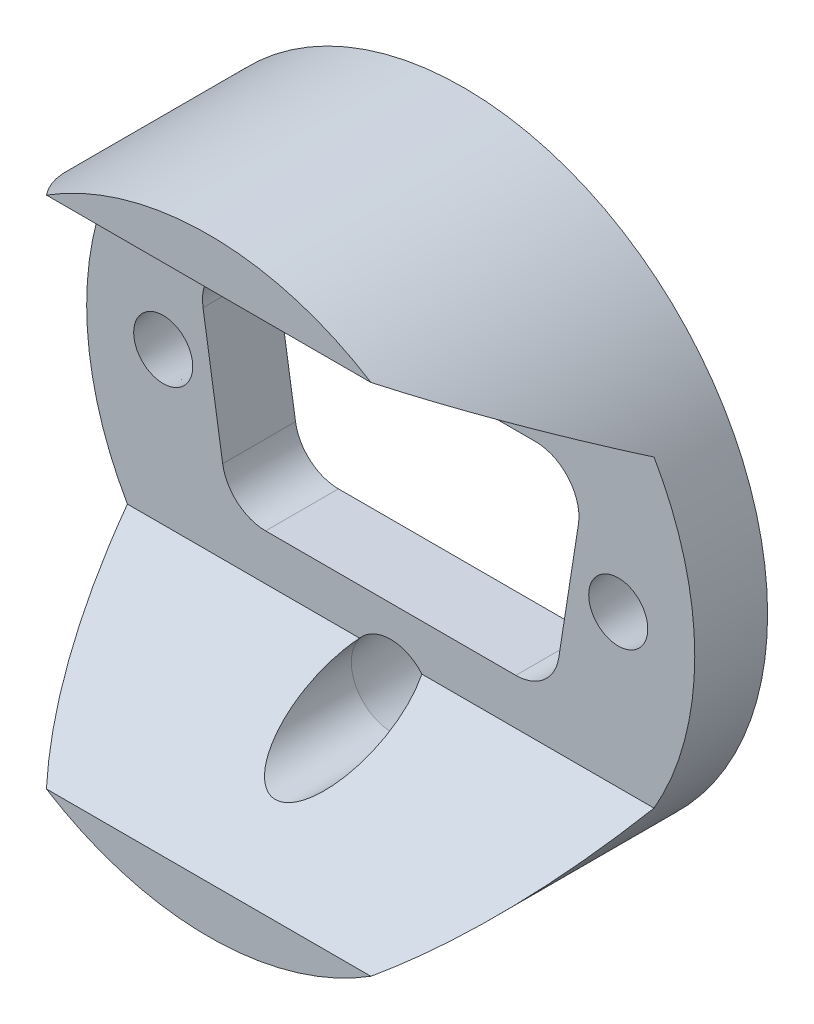
SolidWorks part; units mm, degrees
material "6061-T6 (SS)"
ref_plane "Front Plane" through (0, 0, 0) normal (0, 0, 1) x (1, 0, 0)
ref_plane "Top Plane" through (0, 0, 0) normal (0, 1, 0) x (1, 0, 0)
ref_plane "Right Plane" through (0, 0, 0) normal (1, 0, 0) x (0, 0, -1)
sketch "Sketch1" plane through (0, 0, 0) normal (0, 0, 1) x (1, 0, 0)
  circle A0 centre (0, 0) radius 16.7
  dimension "D1" = 33.4
extrude "Boss-Extrude1" add sketch "Sketch1" along normal blind 14
sketch "Sketch2" plane through (0, 0, 14) normal (0, 0, 1) x (1, 0, 0)
  line L1 (-19.05, -6.35) -> (19.05, -6.35)
  line L2 (-19.05, -6.35) -> (-19.05, 6.35)
  line L3 (-19.05, 6.35) -> (19.05, 6.35)
  line L4 (19.05, -6.35) -> (19.05, 6.35)
  line L5 (-19.05, -6.35) -> (19.05, 6.35) construction
  line L6 (-19.05, 6.35) -> (19.05, -6.35) construction
  point P0 (0, 0)
  dimension "D1" = 12.7
  dimension "D2" = 38.1
extrude "Cut-Extrude1" cut sketch "Sketch2" against normal blind 10
sketch "Sketch3" plane through (0, 0, 4) normal (0, 0, 1) x (1, 0, 0)
  line L0 (-7.9502, 5.8293) -> (7.9502, 5.8293)
  line L1 (10.309, 3.0718) -> (9.2295, -3.8116)
  line L2 (6.8707, -5.8293) -> (-6.8707, -5.8293)
  line L3 (-9.2295, -3.8116) -> (-10.309, 3.0718)
  line L4 (0, 0) -> (0, 5.8293) construction
  line L5 (0, 0) -> (0, -5.8293) construction
  circle A0 centre (-12.4968, -0.0127) radius 2.1844
  circle A1 centre (12.4968, 0) radius 2.1844
  arc A2 (-7.9502, 5.8293) -> (-10.309, 3.0718) centre (-7.9502, 3.4417) ccw
  arc A3 (7.9502, 5.8293) -> (10.309, 3.0718) centre (7.9502, 3.4417) cw
  arc A4 (9.2295, -3.8116) -> (6.8707, -5.8293) centre (6.8707, -3.4417) cw
  arc A5 (-6.8707, -5.8293) -> (-9.2295, -3.8116) centre (-6.8707, -3.4417) cw
  dimension "D1" = 2.3876
  dimension "D8" = 4.3688
  dimension "D2" = 15.9004
  dimension "D3" = 13.7414
  dimension "D4" = 6.8834
  dimension "D5" = 24.9936
  dimension "D6" = 12.4968
  dimension "D7" = 5.842
extrude "Cut-Extrude2" cut sketch "Sketch3" against normal through all contours A5 L2 A4 L1 A3 L0 A2 L3
sketch "Sketch4" plane through (0, 0, 0) normal (0, 0, -1) x (-1, 0, 0)
  line L0 (-13.4743, 5.8293) -> (13.4743, 5.8293) construction
  line L1 (-7.9502, 5.8293) -> (7.9502, 5.8293) construction
  line L4 (-13.4743, -5.8293) -> (13.4743, -5.8293) construction
  line L5 (6.8707, -5.8293) -> (-6.8707, -5.8293) construction
  line L6 (0, 5.8293) -> (0, -5.8293) construction
  circle A0 centre (-12.4968, 0) radius 2.1844
  circle A1 centre (12.4968, -0.0127) radius 2.1844
  arc A6 (-14.6812, 0) -> (-13.4743, -5.8293) centre (0, 0) ccw construction
  arc A7 (-14.6812, 0) -> (-13.4743, 5.8293) centre (0, 0) cw construction
  arc A8 (14.6812, 0) -> (13.4743, 5.8293) centre (0, 0) ccw construction
  arc A9 (14.6812, 0) -> (13.4743, -5.8293) centre (0, 0) cw construction
  circle A12 centre (12.4968, 0) radius 2.1844 construction
  dimension "D1" = 4.3688
extrude "Cut-Extrude9" cut sketch "Sketch4" against normal through all draft 8
ref_plane "Plane1" through (16.7, 0, 0) normal (1, 0, 0) x (0, 0, -1)
sketch "Sketch6" plane through (16.7, 0, 0) normal (1, 0, 0) x (0, 0, -1)
  line L0 (-4, 6.35) -> (-4, 16.7) construction
  line L1 (0, 16.7) -> (-14, 16.7) construction
  line L2 (-4, 8.35) -> (-14, 14.1235)
  line L3 (-14, 16.7) -> (-14, 6.35) construction
  line L4 (-14, 14.1235) -> (-14, 6.35)
  line L5 (-14, 6.35) -> (-4, 6.35) construction
  line L6 (-14, 6.35) -> (-4, 6.35)
  line L7 (-4, 6.35) -> (-4, 8.35)
  line L8 (0, 0) -> (-4, 0) construction
  line L9 (-4, 6.35) -> (-4, -6.35) construction
  line L10 (-4, -6.35) -> (-4, -8.35)
  line L11 (-14, -6.35) -> (-4, -6.35)
  line L12 (-14, -14.1235) -> (-14, -6.35)
  line L13 (-4, -8.35) -> (-14, -14.1235)
  dimension "D1" = 2
  dimension "D2" = 60
extrude "Cut-Extrude10" cut sketch "Sketch6" against normal through all
sketch "Sketch7" plane through (0, 0, 0) normal (0, 0, -1) x (-1, 0, 0)
  line L0 (0, -9.779) -> (0, 9.779) construction
  circle A0 centre (0, 9.779) radius 2.7813
  circle A1 centre (0, -9.779) radius 2.7813
  point P4 (0, 0)
  dimension "D1" = 19.558
  dimension "D2" = 5.5626
extrude "Cut-Extrude11" cut sketch "Sketch7" against normal blind 3.937 draft 8
sketch "Sketch8" plane through (0, 0, 3.937) normal (0, 0, -1) x (-1, 0, 0)
  circle A1 centre (0, -9.779) radius 2.228
  circle A2 centre (0, -9.779) radius 2.228
  circle A3 centre (0, 9.779) radius 2.228
  circle A4 centre (0, 9.779) radius 2.228
  dimension "D1" = 0
  dimension "D2" = 0
extrude "Cut-Extrude12" cut sketch "Sketch8" against normal through all
